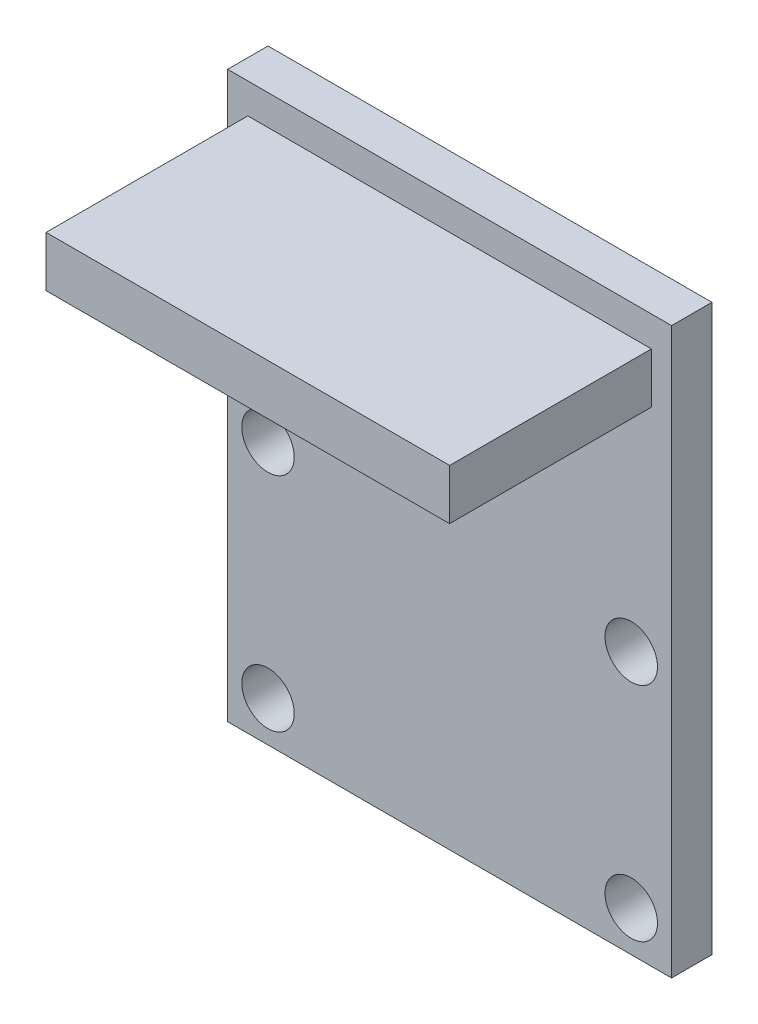
SolidWorks part; units mm, degrees
ref_plane "Front" through (0, 0, 0) normal (0, 0, 1) x (1, 0, 0)
ref_plane "Top" through (0, 0, 0) normal (0, 1, 0) x (1, 0, 0)
ref_plane "Right" through (0, 0, 0) normal (1, 0, 0) x (0, 0, -1)
sketch "草图1" plane through (0, 0, 0) normal (0, 0, 1) x (1, 0, 0)
  line L1 (-11, 14) -> (11, 14)
  line L2 (-11, 14) -> (-11, -14)
  line L3 (-11, -14) -> (11, -14)
  line L4 (11, 14) -> (11, -14)
  line L5 (0, -14) -> (0, 14) construction
  line L6 (-11, 0) -> (11, 0) construction
  line L7 (-9, -0.9979) -> (9, -0.9979) construction
  line L8 (-9, -0.9979) -> (-9, -11.9979) construction
  line L9 (-9, -11.9979) -> (9, -11.9979) construction
  line L10 (9, -0.9979) -> (9, -11.9979) construction
  line L11 (0, -11.9979) -> (0, -0.9979) construction
  line L12 (-9, -6.4979) -> (9, -6.4979) construction
  line L13 (-3, -9.4979) -> (3, -9.4979) construction
  line L14 (-3, -9.4979) -> (-3, -3.4979) construction
  line L15 (-3, -3.4979) -> (3, -3.4979) construction
  line L16 (3, -9.4979) -> (3, -3.4979) construction
  line L17 (-3, -9.4979) -> (3, -3.4979) construction
  line L18 (-3, -3.4979) -> (3, -9.4979) construction
  circle A0 centre (-9, -11.9979) radius 1.3
  circle A1 centre (-9, -0.9979) radius 1.3
  circle A2 centre (9, -0.9979) radius 1.3
  circle A3 centre (9, -11.9979) radius 1.3
  point P13 (0, -6.4979)
  point P70 (0, -6.4979)
  point P92 (0, 0)
  dimension "D5" = 2.6
  dimension "D6" = 2.6
  dimension "D7" = 2.6
  dimension "D8" = 2.6
  dimension "D1" = 22
  dimension "D2" = 28
  dimension "D3" = 11
  dimension "D4" = 18
  dimension "D9" = 0
  dimension "D10" = 0
extrude "凸台-拉伸1" add sketch "草图1" along normal blind 2
sketch "草图2" plane through (0, 0, 2) normal (0, 0, 1) x (1, 0, 0)
  line L0 (-11, 14) -> (-11, -14) construction
  line L1 (-10, 10) -> (10, 10)
  line L2 (-10, 10) -> (-10, 12.5)
  line L3 (-10, 12.5) -> (10, 12.5)
  line L4 (10, 10) -> (10, 12.5)
  line L5 (0, 12.5) -> (0, 0.078) construction
  line L6 (-10, 11.25) -> (10, 11.25) construction
  line L8 (11, 14) -> (-11, 14) construction
  point P96 (0, 11.25)
  dimension "D1" = 20
  dimension "D2" = 2.5
  dimension "D3" = 1.5
  dimension "D4" = 1
extrude "凸台-拉伸2" add sketch "草图2" along normal blind 10
